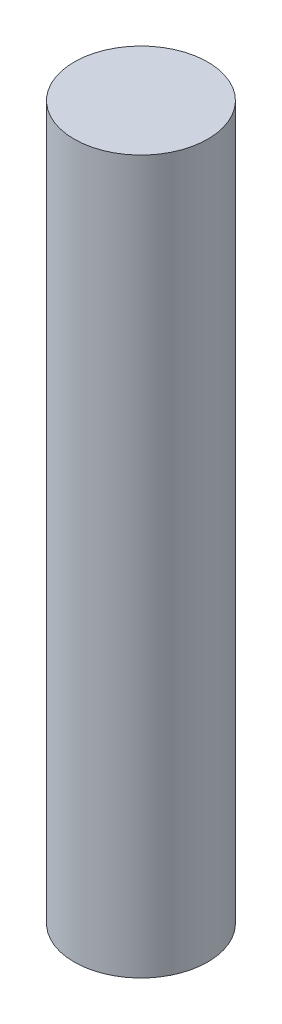
SolidWorks part; units mm, degrees
ref_plane "Front Plane" through (0, 0, 0) normal (0, 0, 1) x (1, 0, 0)
ref_plane "Top Plane" through (0, 0, 0) normal (0, 1, 0) x (1, 0, 0)
ref_plane "Right Plane" through (0, 0, 0) normal (1, 0, 0) x (0, 0, -1)
sketch "Sketch1" plane through (0, 0, 0) normal (0, 1, 0) x (1, 0, 0)
  circle A0 centre (0, 0) radius 1.5
  dimension "D1" = 3
extrude "Boss-Extrude1" add sketch "Sketch1" along normal mid plane 16
